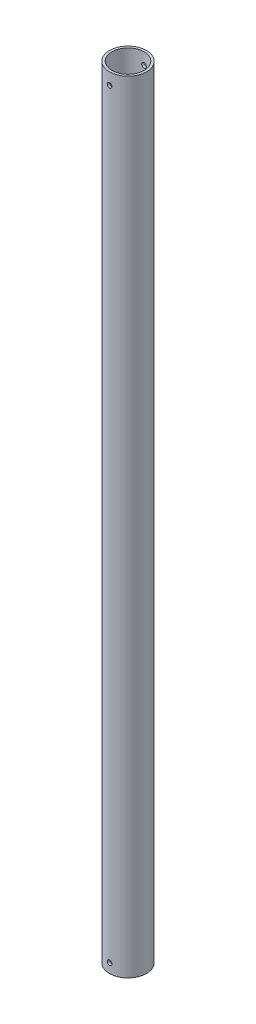
SolidWorks part; units mm, degrees
ref_plane "Front" through (0, 0, 0) normal (0, 0, 1) x (1, 0, 0)
ref_plane "Top" through (0, 0, 0) normal (0, 1, 0) x (1, 0, 0)
ref_plane "Right" through (0, 0, 0) normal (1, 0, 0) x (0, 0, -1)
sketch "Sketch2" plane through (0, 0, 0) normal (0, 1, 0) x (1, 0, 0)
  circle A0 centre (0, 0) radius 24.972
  dimension "D1" = 49.944
extrude "Extrude-Thin1" add sketch "Sketch2" along normal blind 1054.1 thin thin type one direction reverse wall 3.175
sketch "Sketch3" plane through (0, 0, 0) normal (0, 0, 1) x (1, 0, 0)
  line L0 (0, 0) -> (0, 12.7) construction
  line L1 (0, 1054.1) -> (0, 1038.225) construction
  line L4 (24.972, 1054.1) -> (-24.972, 1054.1) construction
  circle A0 centre (0, 12.7) radius 3.175
  circle A2 centre (0, 1038.225) radius 3.175
  dimension "D1" = 6.35
  dimension "D3" = 6.35
  dimension "D2" = 12.7
  dimension "D4" = 15.875
extrude "Cut-Extrude2" cut sketch "Sketch3" against normal through all both and the other way through all
